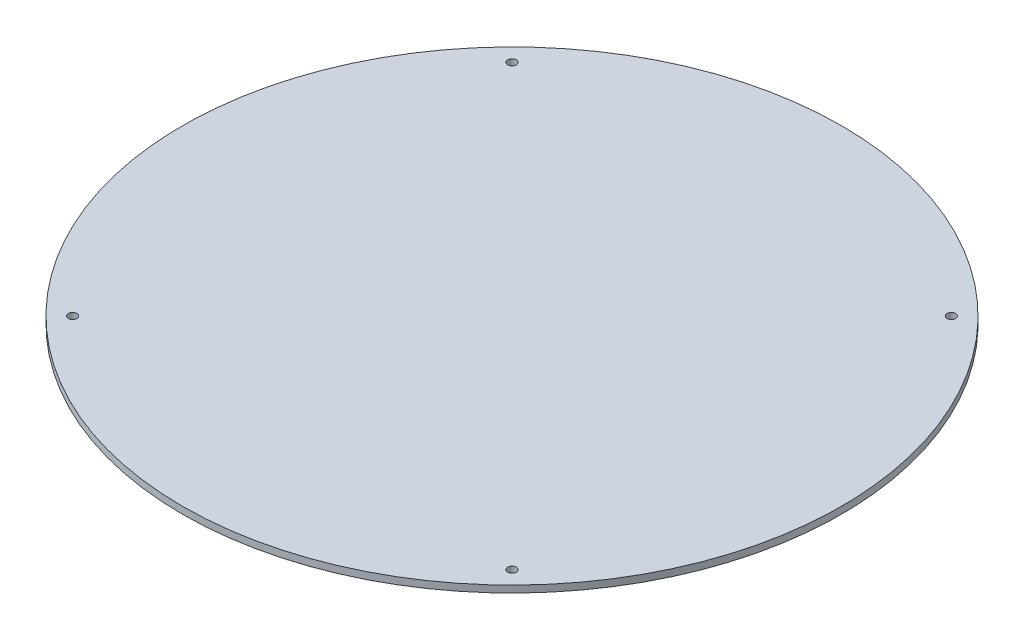
SolidWorks part; units mm, degrees
ref_plane "Front Plane" through (0, 0, 0) normal (0, 0, 1) x (1, 0, 0)
ref_plane "Top Plane" through (0, 0, 0) normal (0, 1, 0) x (1, 0, 0)
ref_plane "Right Plane" through (0, 0, 0) normal (1, 0, 0) x (0, 0, -1)
sketch "Sketch1" plane through (0, 0, 0) normal (0, 1, 0) x (1, 0, 0)
  line L0 (0, 0) -> (0, 76.2) construction
  line L1 (0, 0) -> (76.2, 0) construction
  line L2 (0, 0) -> (0, -76.2) construction
  line L3 (0, 0) -> (-76.2, 0) construction
  circle A0 centre (0, 0) radius 76.2
  circle A1 centre (50.8, 50.8) radius 1
  circle A2 centre (-50.8, 50.8) radius 1
  circle A3 centre (50.8, -50.8) radius 1
  circle A4 centre (-50.8, -50.8) radius 1
  dimension "D1" = 152.4
  dimension "D3" = 50.8
  dimension "D4" = 2
  dimension "D2" = 50.8
extrude "Boss-Extrude1" add sketch "Sketch1" along normal blind 1.6
